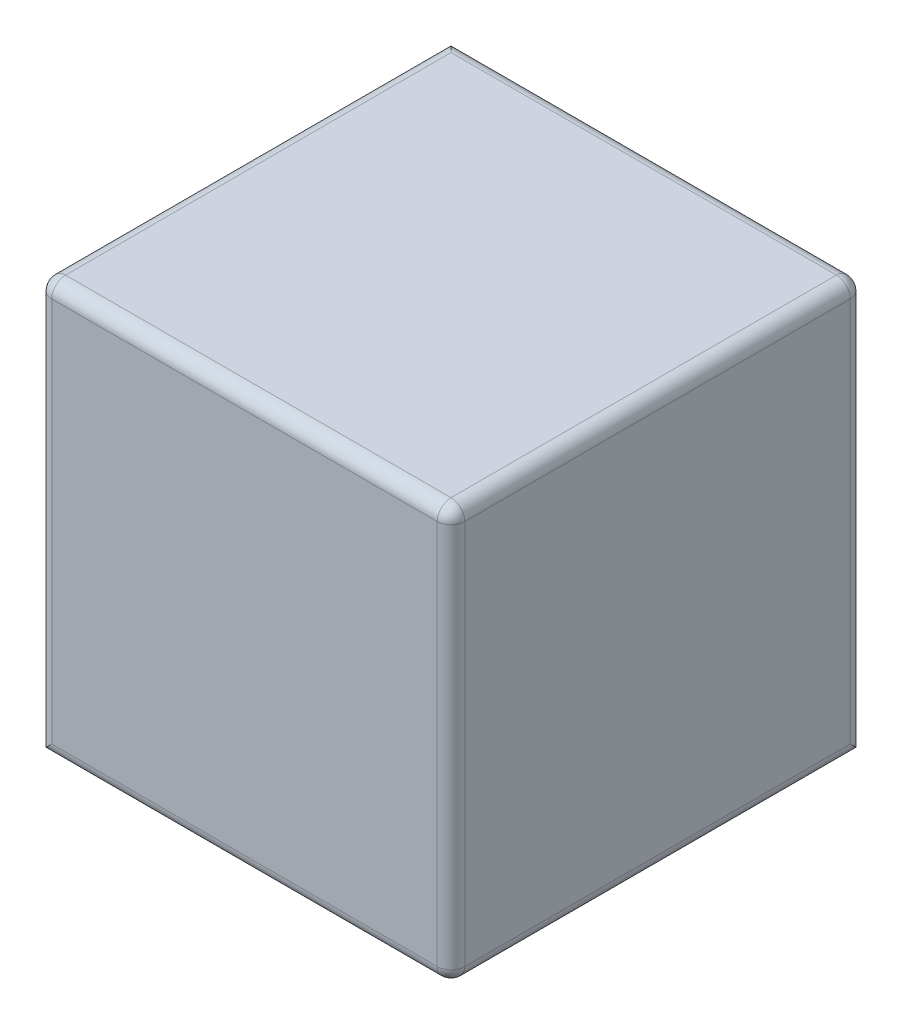
SolidWorks part; units mm, degrees
ref_plane "Front Plane" through (0, 0, 0) normal (0, 0, 1) x (1, 0, 0)
ref_plane "Top Plane" through (0, 0, 0) normal (0, 1, 0) x (1, 0, 0)
ref_plane "Right Plane" through (0, 0, 0) normal (1, 0, 0) x (0, 0, -1)
sketch "Sketch1" plane through (0, 0, 0) normal (0, 0, 1) x (1, 0, 0)
  line L1 (-150, -150) -> (150, -150)
  line L2 (-150, -150) -> (-150, 150)
  line L3 (-150, 150) -> (150, 150)
  line L4 (150, -150) -> (150, 150)
  line L5 (-150, -150) -> (150, 150) construction
  line L6 (-150, 150) -> (150, -150) construction
  point P0 (0, 0)
  dimension "D1" = 300
  dimension "D2" = 300
extrude "Boss-Extrude1" add sketch "Sketch1" along normal blind 300
fillet "Fillet1" radius 10 9 edges at (150, 0, 0) (0, 150, 0) (150, 0, 300) (0, 150, 300) (-150, 0, 300) (0, -150, 300) (150, -150, 150) (-150, 150, 150) (150, 150, 150)
